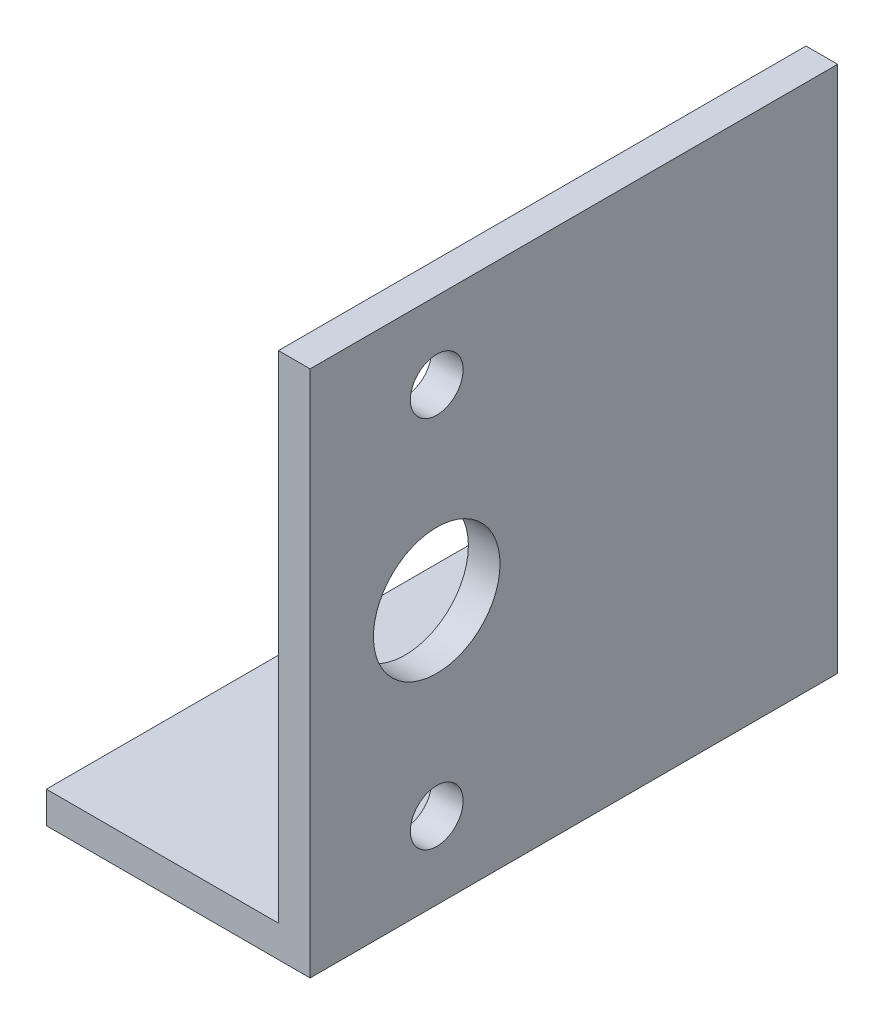
SolidWorks part; units mm, degrees
material "AISI 1020"
ref_plane "Alzado" through (0, 0, 0) normal (0, 0, 1) x (1, 0, 0)
ref_plane "Planta" through (0, 0, 0) normal (0, 1, 0) x (1, 0, 0)
ref_plane "Vista lateral" through (0, 0, 0) normal (1, 0, 0) x (0, 0, -1)
sketch "Croquis1" plane through (0, 0, 0) normal (0, 0, 1) x (1, 0, 0)
  line L0 (-25, 0) -> (0, 0)
  line L1 (0, 0) -> (0, 50)
  line L2 (-25, 3) -> (-3, 3)
  line L3 (-3, 3) -> (-3, 50)
  line L4 (-25, 3) -> (-25, 0)
  line L5 (-3, 50) -> (0, 50)
  dimension "D1" = 50
  dimension "D2" = 25
  dimension "D3" = 3
extrude "Saliente-Extruir1" add sketch "Croquis1" along normal blind 50
sketch "Croquis2" plane through (0, 0, 0) normal (1, 0, 0) x (0, 0, -1)
  line L0 (-38, 50) -> (-38, 0) construction
  line L1 (-50, 50) -> (0, 50) construction
  line L2 (-50, 0) -> (0, 0) construction
  line L3 (-50, 0) -> (-50, 50) construction
  line L4 (-50, 25) -> (0, 25) construction
  line L5 (0, 0) -> (0, 50) construction
  circle A0 centre (-38, 25) radius 6
  circle A1 centre (-38, 42.7) radius 2.5
  circle A2 centre (-38, 7.3) radius 2.5
  dimension "D3" = 12
  dimension "D6" = 5
  dimension "D1" = 12
  dimension "D2" = 25
  dimension "D4" = 35.4
  dimension "D5" = 17.7
extrude "Cortar-Extruir1" cut sketch "Croquis2" against normal up to surface (3 mm away) up to face at (-3, 26.5, 25)
equation "\"D5@Croquis2\"=\"D4@Croquis2\"/2"
